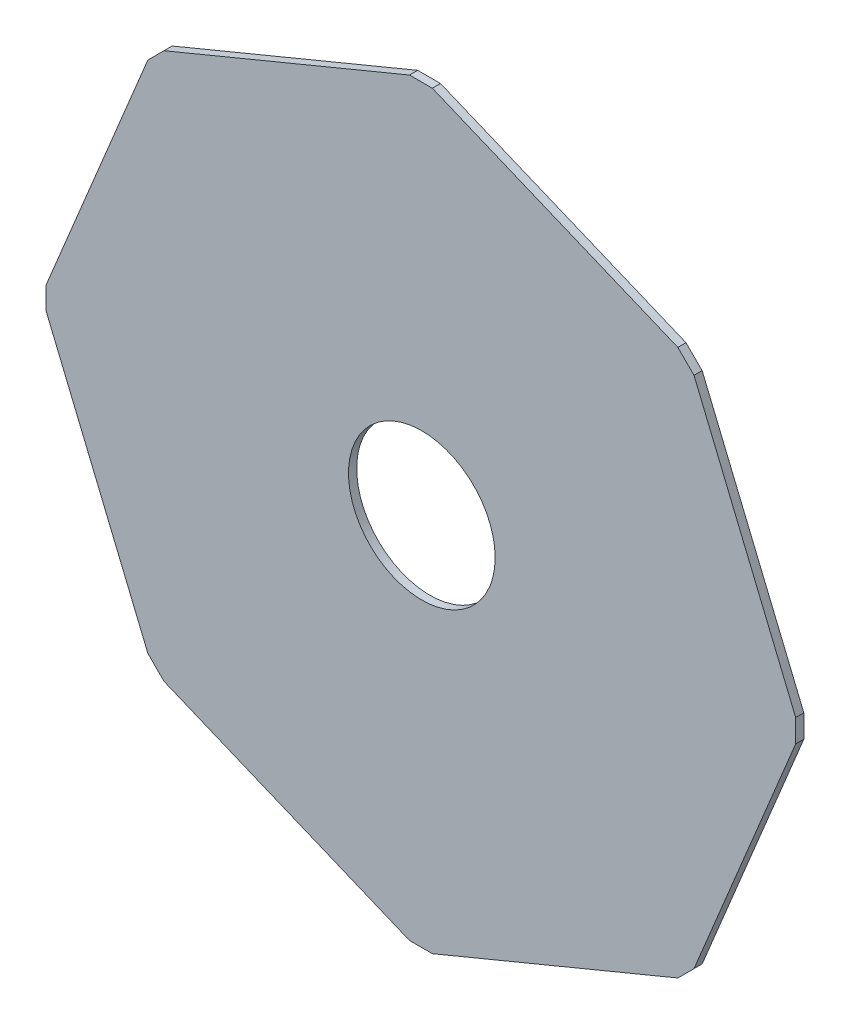
SolidWorks part; units mm, degrees
ref_plane "Front Plane" through (0, 0, 0) normal (0, 0, 1) x (1, 0, 0)
ref_plane "Top Plane" through (0, 0, 0) normal (0, 1, 0) x (1, 0, 0)
ref_plane "Right Plane" through (0, 0, 0) normal (1, 0, 0) x (0, 0, -1)
sketch "Sketch1" plane through (0, 0, 0) normal (0, 0, 1) x (1, 0, 0)
  line L0 (-230.5579, -6.721) -> (-168.1422, -157.4058)
  line L1 (-168.1422, -157.4058) -> (-158.2428, -167.3053)
  line L2 (-158.2428, -167.3053) -> (-7.5579, -229.721)
  line L3 (-7.5579, -229.721) -> (6.4421, -229.721)
  line L4 (6.4421, -229.721) -> (157.1269, -167.3053)
  line L5 (157.1269, -167.3053) -> (167.0264, -157.4058)
  line L6 (167.0264, -157.4058) -> (229.4421, -6.721)
  line L7 (229.4421, -6.721) -> (229.4421, 7.279)
  line L8 (229.4421, 7.279) -> (167.0264, 157.9638)
  line L9 (167.0264, 157.9638) -> (157.1269, 167.8633)
  line L10 (157.1269, 167.8633) -> (6.4421, 230.279)
  line L11 (6.4421, 230.279) -> (-7.5579, 230.279)
  line L12 (-7.5579, 230.279) -> (-158.2428, 167.8633)
  line L13 (-158.2428, 167.8633) -> (-168.1422, 157.9638)
  line L14 (-168.1422, 157.9638) -> (-230.5579, 7.279)
  line L15 (-230.5579, 7.279) -> (-230.5579, -6.721)
  circle A0 centre (0, 0) radius 45
  dimension "D3" = 90
  dimension "D1" = 150.6848
  dimension "D2" = 163.1001
extrude "Boss-Extrude1" add sketch "Sketch1" along normal blind 5
